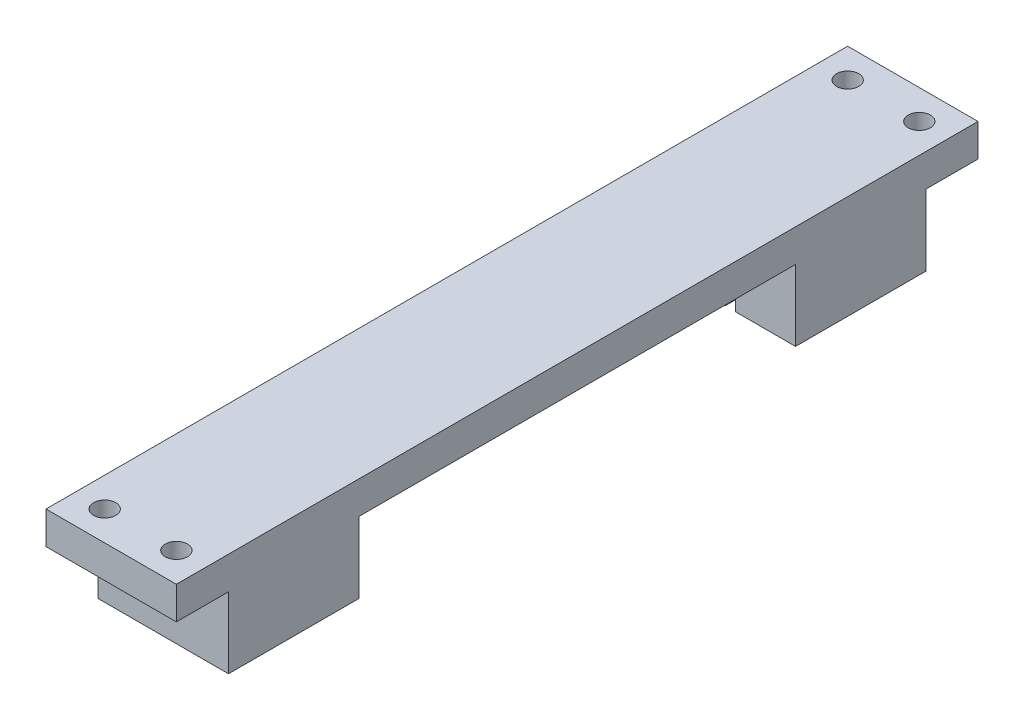
SolidWorks part; units mm, degrees
ref_plane "Front Plane" through (0, 0, 0) normal (0, 0, 1) x (1, 0, 0)
ref_plane "Top Plane" through (0, 0, 0) normal (0, 1, 0) x (1, 0, 0)
ref_plane "Right Plane" through (0, 0, 0) normal (1, 0, 0) x (0, 0, -1)
sketch "Sketch1" plane through (0, 0, 0) normal (0, 1, 0) x (1, 0, 0)
  line L1 (-10, -14) -> (10, -14)
  line L2 (-10, -14) -> (-10, 14)
  line L3 (-10, 14) -> (10, 14)
  line L4 (10, -14) -> (10, 14)
  line L5 (-10, -14) -> (10, 14) construction
  line L6 (-10, 14) -> (10, -14) construction
  point P0 (0, 0)
  dimension "D1" = 20
  dimension "D2" = 28
extrude "Boss-Extrude1" add sketch "Sketch1" along normal blind 5 contours L4 L3 L2 L1
sketch "Sketch2" plane through (0, 0, 0) normal (0, -1, 0) x (-1, 0, 0)
  line L0 (10, -14) -> (10, 14) construction
  line L1 (-10, 14) -> (10, 14)
  line L2 (-10, 14) -> (-10, -6)
  line L3 (-10, -6) -> (10, -6)
  line L4 (10, 14) -> (10, -6)
  dimension "D1" = 20
extrude "Boss-Extrude2" add sketch "Sketch2" along normal blind 10.9
sketch "Sketch3" plane through (0, -10.9, 0) normal (0, -1, 0) x (-1, 0, 0)
  line L0 (10, 14) -> (-10, 14) construction
  line L1 (-0.8, 14) -> (0.8, 14)
  line L2 (-0.8, 14) -> (-0.8, -1)
  line L3 (-0.8, -1) -> (0.8, -1)
  line L4 (0.8, 14) -> (0.8, -1)
  line L5 (-10, 14) -> (-10, -6) construction
  dimension "D1" = 1.6
  dimension "D2" = 15
  dimension "D3" = 9.2
extrude "Cut-Extrude1" cut sketch "Sketch3" against normal blind 10.9
hole_wizard "M3 Clearance Hole1" positions "Sketch5" profile "Sketch4" hole size "M3" standard "ANSI Metric"
sketch "Sketch5" plane through (0, 0, 0) normal (0, -1, 0) x (-1, 0, 0)
  line L0 (-10, -6) -> (10, -6) construction
  line L2 (-10, -14) -> (-10, -6) construction
  line L3 (10, -14) -> (10, -6) construction
  point P1 (-5.5, -9.5)
  point P3 (5.5, -9.5)
  dimension "D1" = 3.5
  dimension "D2" = 3.5
  dimension "D3" = 4.5
  dimension "D4" = 4.5
sketch "Sketch4" plane through (5.5, 0, 9.5) normal (1, 0, 0) x (0, 0, -1)
  line L0 (0, 0) -> (0, 6.0205)
  line L1 (0, 6.0205) -> (1.7, 4.999)
  line L2 (1.7, 4.999) -> (1.7, 0)
  line L5 (1.7, 0) -> (0, 0)
  line L10 (0, 6.0205) -> (-1.7, 4.999) construction
  line L11 (0, -6.35) -> (0, 107.95) construction
  dimension "Hole Dia." = 3.4
  dimension "Hole Depth" = 4.999
  dimension "Drill Angle" = 118
sketch "Sketch6" plane through (0, 0, -14) normal (0, 0, -1) x (-1, 0, 0)
  line L0 (-10, 5) -> (-10, -10.9) construction
  line L1 (10, 5) -> (-10, 5)
  line L2 (10, 5) -> (10, 0)
  line L3 (10, 0) -> (-10, 0)
  line L4 (-10, 5) -> (-10, 0)
extrude "Boss-Extrude3" add sketch "Sketch6" along normal blind 87
sketch "Sketch7" plane through (0, 0, -101) normal (0, 0, -1) x (-1, 0, 0)
  line L1 (-10, 5) -> (10, 5)
  line L2 (-10, 5) -> (-10, 0)
  line L3 (-10, 0) -> (10, 0)
  line L4 (10, 5) -> (10, 0)
extrude "Boss-Extrude4" add sketch "Sketch7" along normal blind 8
sketch "Sketch8" plane through (0, 0, 0) normal (0, -1, 0) x (-1, 0, 0)
  line L1 (-10, 109) -> (-10, 14) construction
  line L2 (-10, 81) -> (10, 81)
  line L3 (-10, 81) -> (-10, 101)
  line L5 (-10, 101) -> (10, 101)
  line L6 (10, 81) -> (10, 101)
  line L7 (10, 109) -> (10, 14) construction
  line L8 (-10, 109) -> (10, 109) construction
  dimension "D1" = 20
  dimension "D2" = 8
extrude "Boss-Extrude5" add sketch "Sketch8" along normal blind 10.9
sketch "Sketch9" plane through (0, -10.9, 0) normal (0, -1, 0) x (-1, 0, 0)
  line L1 (0.8, 60) -> (-0.8, 60)
  line L2 (0.8, 60) -> (0.8, 88.5)
  line L3 (0.8, 88.5) -> (-0.8, 88.5)
  line L4 (-0.8, 60) -> (-0.8, 88.5)
  line L9 (-10, 101) -> (-10, 81) construction
  line L10 (10, 101) -> (-10, 101) construction
  dimension "D1" = 1.6
  dimension "D2" = 9.2
  dimension "D3" = 12.5
extrude "Cut-Extrude2" cut sketch "Sketch9" against normal blind 10.9
hole_wizard "M3 Clearance Hole2" positions "Sketch11" profile "Sketch10" hole size "M3" standard "ANSI Metric" end condition through all
sketch "Sketch11" plane through (0, 0, 0) normal (0, -1, 0) x (-1, 0, 0)
  line L0 (10, 101) -> (-10, 101) construction
  line L1 (-10, 109) -> (-10, 101) construction
  line L2 (10, 109) -> (10, 101) construction
  point P0 (-5.5, 104.5)
  point P2 (5.5, 104.5)
  dimension "D1" = 3.5
  dimension "D2" = 3.5
  dimension "D3" = 4.5
  dimension "D4" = 4.5
sketch "Sketch10" plane through (5.5, 0, -104.5) normal (1, 0, 0) x (0, 0, -1)
  line L0 (0, 0) -> (0, 5)
  line L1 (0, 5) -> (1.7, 5)
  line L2 (1.7, 5) -> (1.7, 0)
  line L5 (1.7, 0) -> (0, 0)
  line L11 (0, -6.35) -> (0, 107.95) construction
  dimension "Thru Hole Dia." = 3.4
  dimension "Thru Hole Depth" = 5
